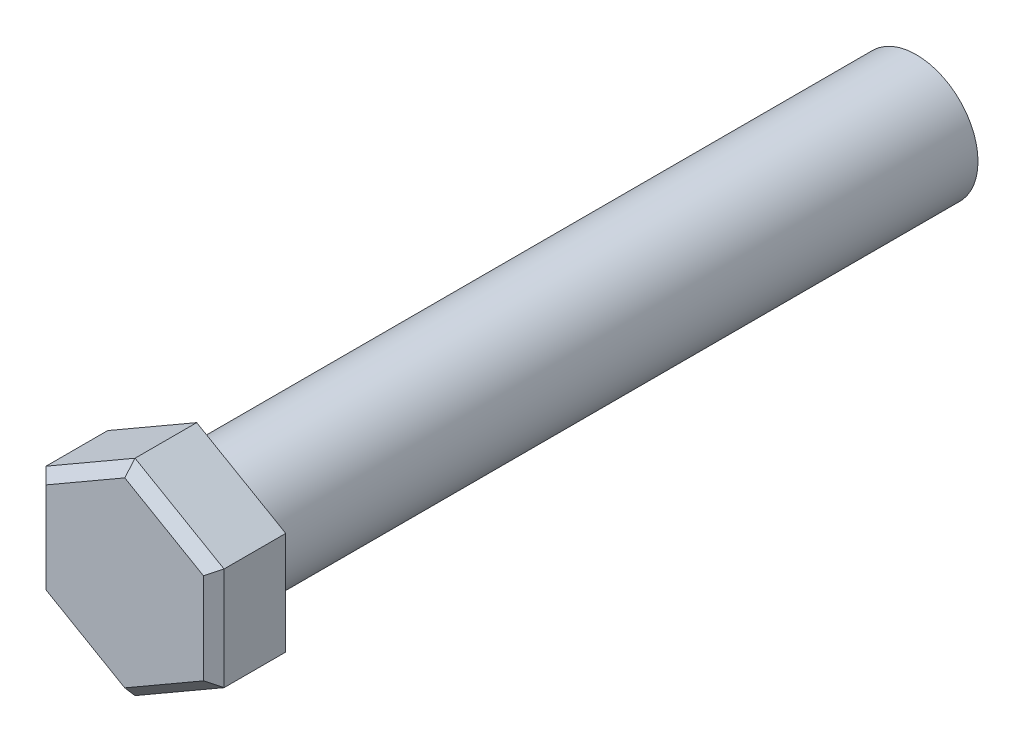
SolidWorks part; units mm, degrees
ref_plane "Alzado" through (0, 0, 0) normal (0, 0, 1) x (1, 0, 0)
ref_plane "Planta" through (0, 0, 0) normal (0, 1, 0) x (1, 0, 0)
ref_plane "Vista lateral" through (0, 0, 0) normal (1, 0, 0) x (0, 0, -1)
sketch "Croquis1" plane through (0, 0, 0) normal (0, 0, 1) x (1, 0, 0)
  circle A0 centre (0, 0) radius 6
  dimension "D1" = 12
extrude "Saliente-Extruir3" add sketch "Croquis1" along normal blind 70
sketch "Croquis3" plane through (0, 0, 70) normal (0, 0, 1) x (1, 0, 0)
  line L0 (0, 0) -> (0, 2.1215)
  line L1 (0, 10) -> (-8.6603, 5)
  line L2 (-8.6603, 5) -> (-8.6603, -5)
  line L3 (-8.6603, -5) -> (0, -10)
  line L4 (0, -10) -> (8.6603, -5)
  line L5 (8.6603, -5) -> (8.6603, 5)
  line L6 (8.6603, 5) -> (0, 10)
  line L7 (0, 2.1215) -> (0, 0)
  line L9 (10, 0) -> (8.6603, 0)
  line L11 (-8.6603, 0) -> (-10, 0)
  arc A0 (-6.141, -7.8923) -> (0, -10) centre (0, 0) ccw
  dimension "D1" = 20
extrude "Saliente-Extruir4" add sketch "Croquis3" along normal blind 7
chamfer "Chaflán1" distance 1 angle 45 6 edges at (8.6603, 0, 77) (4.3301, -7.5, 77) (-4.3301, -7.5, 77) (-8.6603, 0, 77) (-4.3301, 7.5, 77) (4.3301, 7.5, 77)
fillet "Redondeo1" radius 1 1 edges at (6, 0, 70)
sketch "Croquis8" plane through (0, 0, 0) normal (0, 0, -1) x (-1, 0, 0)
  circle A0 centre (0, 0) radius 6.0521
